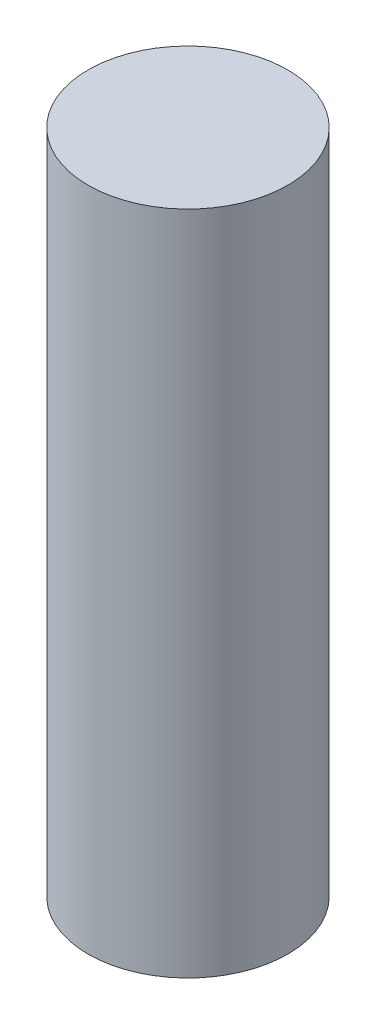
SolidWorks part; units mm, degrees
ref_plane "Front Plane" through (0, 0, 0) normal (0, 0, 1) x (1, 0, 0)
ref_plane "Top Plane" through (0, 0, 0) normal (0, 1, 0) x (1, 0, 0)
ref_plane "Right Plane" through (0, 0, 0) normal (1, 0, 0) x (0, 0, -1)
sketch "Sketch1" plane through (0, 0, 0) normal (0, 1, 0) x (1, 0, 0)
  circle A0 centre (0, 0) radius 3.048
extrude "Boss-Extrude1" add sketch "Sketch1" along normal blind 20.32
